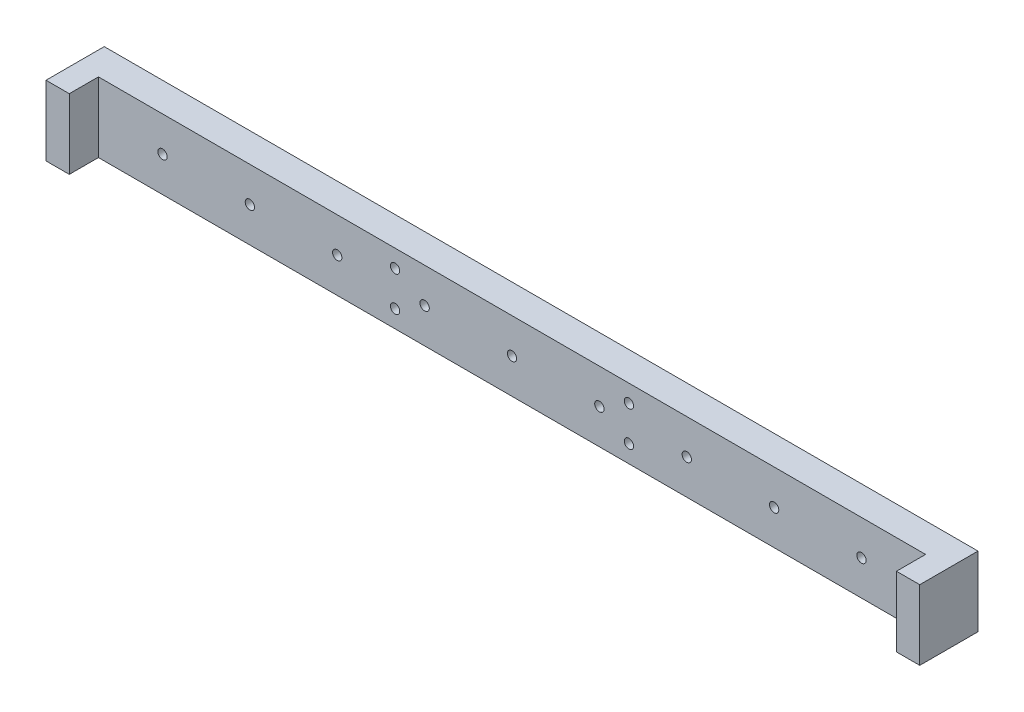
SolidWorks part; units mm, degrees
ref_plane "前视基准面" through (0, 0, 0) normal (0, 0, 1) x (1, 0, 0)
ref_plane "上视基准面" through (0, 0, 0) normal (0, 1, 0) x (1, 0, 0)
ref_plane "右视基准面" through (0, 0, 0) normal (1, 0, 0) x (0, 0, -1)
sketch "草图1" plane through (0, 0, 0) normal (0, 0, 1) x (1, 0, 0)
  line L1 (75, -6) -> (-75, -6)
  line L2 (75, -6) -> (75, 6)
  line L3 (75, 6) -> (-75, 6)
  line L4 (-75, -6) -> (-75, 6)
  line L5 (75, -6) -> (-75, 6) construction
  line L6 (75, 6) -> (-75, -6) construction
  point P0 (0, 0)
  dimension "D1" = 150
  dimension "D2" = 12
extrude "凸台-拉伸1" add sketch "草图1" along normal blind 5
sketch "草图2" plane through (0, 0, 5) normal (0, 0, 1) x (1, 0, 0)
  line L0 (-75, 6) -> (-71, 6)
  line L1 (75, 6) -> (-75, 6) construction
  line L2 (-71, 6) -> (-71, -6)
  line L3 (-75, -6) -> (75, -6) construction
  line L4 (-71, -6) -> (-75, -6)
  line L5 (-75, -6) -> (-75, 6)
  dimension "D1" = 4
extrude "凸台-拉伸2" add sketch "草图2" along normal blind 5
mirror "镜向1" about plane through (0, 0, 0) normal (1, 0, 0) of "凸台-拉伸2"
hole_wizard "M2 螺纹孔2" positions "草图23" profile "草图24" tap size "M2" standard "GB"
sketch "草图23" plane through (0, 0, 0) normal (0, 0, -1) x (-1, 0, 0)
  point P0 (-20.075, -3)
  point P3 (-20.075, 3)
  point P17 (20.075, -3)
  point P20 (20.075, 3)
sketch "草图24" plane through (20.075, -3, 0) normal (1, 0, 0) x (0, 1, 0)
  line L0 (0, 0) -> (0, 5.6807)
  line L1 (0, 5.6807) -> (0.8, 5.2)
  line L2 (0.8, 5.2) -> (0.8, 0)
  line L5 (0.8, 0) -> (0, 0)
  line L10 (0, 5.6807) -> (-0.8, 5.2) construction
  line L11 (0, -6.35) -> (0, 107.95) construction
  dimension "螺纹孔钻头直径" = 1.6
  dimension "螺纹孔钻头深度" = 5.2
  dimension "导头角度" = 118
cosmetic thread "孔螺蚊线17" parameters "D1"=4, "D2"=2
cosmetic thread "孔螺蚊线18" parameters "D1"=4, "D2"=2
cosmetic thread "孔螺蚊线19" parameters "D1"=4, "D2"=2
cosmetic thread "孔螺蚊线20" parameters "D1"=4, "D2"=2
hole_wizard "M2 螺纹孔3" positions "草图25" profile "草图27" tap size "M2" standard "GB" end condition through all
sketch "草图25" plane through (0, 0, 0) normal (0, 0, -1) x (-1, 0, 0)
  point P0 (0, 0)
sketch "草图27" plane through (0, 0, 0) normal (1, 0, 0) x (0, 1, 0)
  line L0 (0, 0) -> (0, 10)
  line L1 (0, 10) -> (0.8, 10)
  line L2 (0.8, 10) -> (0.8, 0)
  line L5 (0.8, 0) -> (0, 0)
  line L11 (0, -6.35) -> (0, 107.95) construction
  dimension "通孔螺纹孔钻头直径" = 1.6
  dimension "通孔螺纹孔钻头深度" = 10
cosmetic thread "孔螺蚊线21" parameters "D2"=2
hole_wizard "M2 螺纹孔4" positions "草图28" profile "草图29" tap size "M2" standard "GB" end condition through all
sketch "草图28" plane through (0, 0, 5) normal (0, 0, 1) x (1, 0, 0)
  point P0 (0, 0)
  point P3 (15, 0)
  point P6 (30, 0)
  point P9 (-30, 0)
  point P12 (-45, 0)
  point P15 (-60, 0)
  point P18 (-15, 0)
  point P21 (45, 0)
  point P24 (60, 0)
sketch "草图29" plane through (0, 0, 5) normal (1, 0, 0) x (0, -1, 0)
  line L0 (0, 0) -> (0, 5)
  line L1 (0, 5) -> (0.8, 5)
  line L2 (0.8, 5) -> (0.8, 0)
  line L5 (0.8, 0) -> (0, 0)
  line L11 (0, -6.35) -> (0, 107.95) construction
  dimension "通孔螺纹孔钻头直径" = 1.6
  dimension "通孔螺纹孔钻头深度" = 5
cosmetic thread "孔螺蚊线23" parameters "D2"=2
cosmetic thread "孔螺蚊线24" parameters "D2"=2
cosmetic thread "孔螺蚊线25" parameters "D2"=2
cosmetic thread "孔螺蚊线26" parameters "D2"=2
cosmetic thread "孔螺蚊线27" parameters "D2"=2
cosmetic thread "孔螺蚊线28" parameters "D2"=2
cosmetic thread "孔螺蚊线29" parameters "D2"=2
cosmetic thread "孔螺蚊线30" parameters "D2"=2
